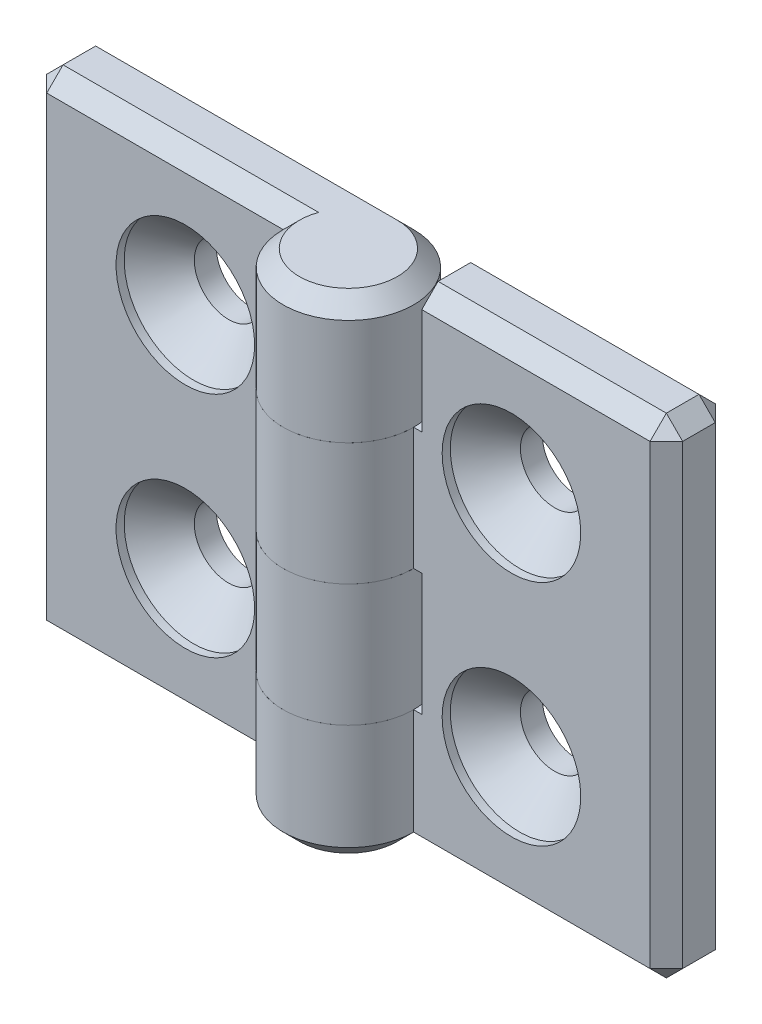
SolidWorks part; units mm, degrees
material "Нейлон"
ref_plane "Спереди" through (0, 0, 0) normal (0, 0, 1) x (1, 0, 0)
ref_plane "Сверху" through (0, 0, 0) normal (0, 1, 0) x (1, 0, 0)
ref_plane "Справа" through (0, 0, 0) normal (1, 0, 0) x (0, 0, -1)
sketch "Эскиз1" plane through (0, 0, 0) normal (0, 1, 0) x (1, 0, 0)
  line L0 (0, 4) -> (-19.5, 4)
  line L1 (-19.5, 4) -> (-19.5, 0)
  line L3 (-19.5, 0) -> (-4, 0)
  line L4 (0, 0) -> (0, 10.5526) construction
  arc A0 (-4, 0) -> (0, 4) centre (0, 0) ccw
  point P1 (0, 0)
  dimension "D1" = 39
  dimension "D2" = 4
extrude "Бобышка-Вытянуть1" add sketch "Эскиз1" along normal mid plane 30
sketch "Эскиз3" plane through (0, 0, 0) normal (0, 0, 1) x (1, 0, 0)
  line L0 (4, -15) -> (4, 15) construction
  line L1 (-4.5, 7.5) -> (4, 7.5)
  line L2 (-4.5, 7.5) -> (-4.5, 0)
  line L3 (-4.5, 0) -> (4, 0)
  line L4 (4, 7.5) -> (4, 0)
  line L5 (4, 0) -> (4, -7.5) construction
  line L6 (4, -15) -> (-4.5, -15)
  line L7 (4, -15) -> (4, -7.5)
  line L8 (4, -7.5) -> (-4.5, -7.5)
  line L9 (-4.5, -15) -> (-4.5, -7.5)
  line L10 (4, 7.5) -> (4, 15) construction
  line L11 (-4, 15) -> (-4, -15) construction
  dimension "D1" = 0.5
extrude "Вырез-Вытянуть1" cut sketch "Эскиз3" against normal through all and the other way through all
hole_wizard "Зенковка для винта с полупотайной головкой M41" positions "Эскиз4" profile "Эскиз6" countersink size "M4" standard "ISO" end condition through all
sketch "Эскиз4" plane through (0, 0, 0) normal (0, 0, 1) x (1, 0, 0)
  line L0 (-10, 7) -> (-10, -7)
  line L2 (0, 0) -> (0, 18.9001) construction
  line L3 (4, 0) -> (-4, 0) construction
  point P0 (-10, 7)
  point P2 (-10, -7)
  point P9 (-10, 0)
  dimension "D1" = 14
  dimension "D2" = 20
sketch "Эскиз6" plane through (-10, 7, 0) normal (1, 0, 0) x (0, -1, 0)
  line L0 (0, 0) -> (0, 4)
  line L1 (0, 4) -> (2.1, 4)
  line L2 (2.1, 4) -> (2.1, 2.65)
  line L3 (2.1, 2.65) -> (4.25, 0.5)
  line L4 (4.25, 0.5) -> (4.25, 0)
  line L6 (4.25, 0) -> (0, 0)
  line L7 (-2.1, 2.65) -> (-4.25, 0.5) construction
  line L11 (0, -6.35) -> (0, 107.95) construction
  dimension "Диаметр сквозного отверстия" = 4.2
  dimension "Глубина сквозного отверстия" = 4
  dimension "Диаметр зенковки" = 8.5
  dimension "Угол зенковки" = 90
  dimension "Утопленность" = 0.5
chamfer "Фаска1" distance 1 angle 45 9 edges at (-12, -15, 0) (-19.5, 0, 0) (-11.75, 15, 0) (-19.5, -15, -2) (-19.5, 15, -2) (2.8284, 15, 2.8284) (-9.75, 15, -4) (-19.5, 0, -4) (-12, -15, -4)
sketch "Угол раскрытия" plane through (0, 0, 0) normal (0, 1, 0) x (1, 0, 0)
  line L0 (0, 0) -> (0, -10)
  line L7 (0, 4) -> (-19.5, 4) construction
  dimension "D1" = 10
  dimension "D2" = 90
pattern_circular "Круговой массив1" count 2 over 360 about axis through (0, 0, 0) along (0, 0, 1) of bodies 106
